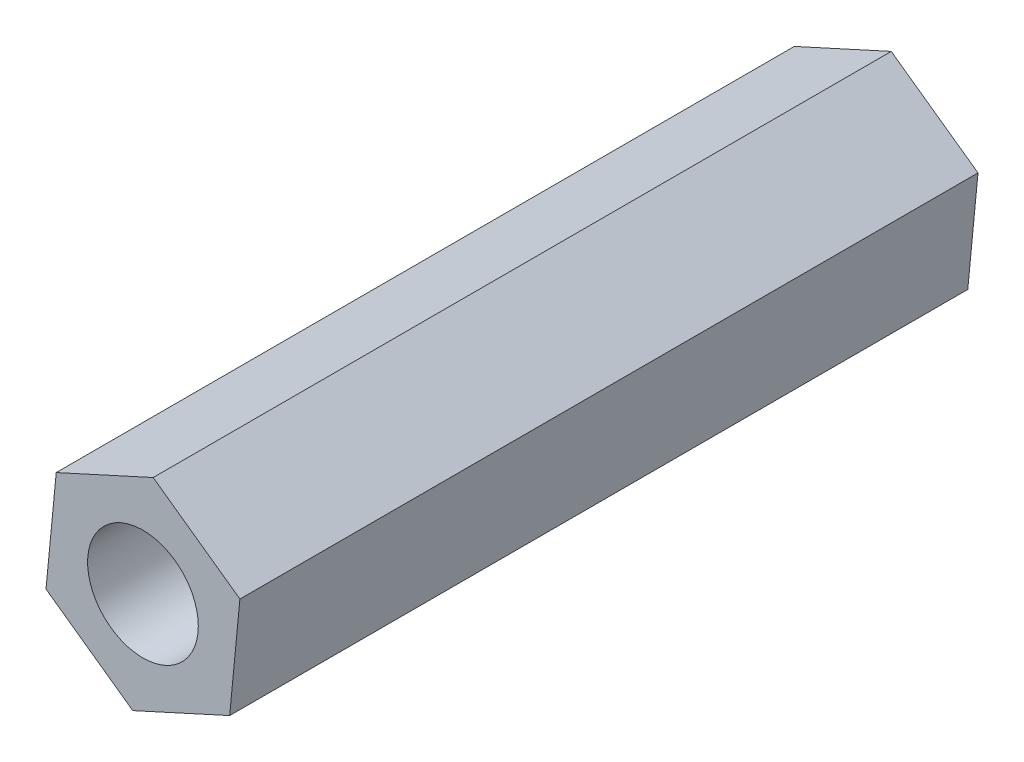
SolidWorks part; units mm, degrees
material "Mosiądz"
ref_plane "Płaszczyzna przednia" through (0, 0, 0) normal (0, 0, 1) x (1, 0, 0)
ref_plane "Płaszczyzna górna" through (0, 0, 0) normal (0, 1, 0) x (1, 0, 0)
ref_plane "Płaszczyzna prawa" through (0, 0, 0) normal (1, 0, 0) x (0, 0, -1)
sketch "Szkic1" plane through (0, 0, 0) normal (0, 0, 1) x (1, 0, 0)
  line L1 (2.627, 1.1967) -> (0.2771, 2.8734)
  line L2 (0.2771, 2.8734) -> (-2.3499, 1.6767)
  line L3 (-2.3499, 1.6767) -> (-2.627, -1.1967)
  line L4 (-2.627, -1.1967) -> (-0.2771, -2.8734)
  line L5 (-0.2771, -2.8734) -> (2.3499, -1.6767)
  line L6 (2.3499, -1.6767) -> (2.627, 1.1967)
  circle A0 centre (0, 0) radius 2.5 construction
  circle A1 centre (0, 0) radius 1.5
  dimension "D2" = 3
  dimension "D1" = 5
extrude "Dodanie-wyciągnięcie1" add sketch "Szkic1" along normal blind 20
